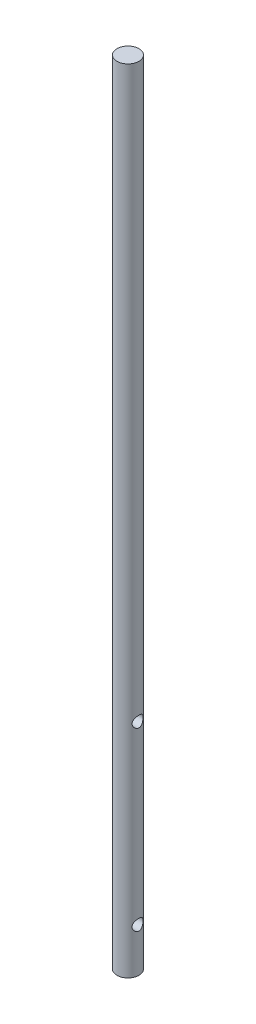
SolidWorks part; units mm, degrees
ref_plane "Front Plane" through (0, 0, 0) normal (0, 0, 1) x (1, 0, 0)
ref_plane "Top Plane" through (0, 0, 0) normal (0, 1, 0) x (1, 0, 0)
ref_plane "Right Plane" through (0, 0, 0) normal (1, 0, 0) x (0, 0, -1)
sketch "Sketch1" plane through (0, 0, 0) normal (0, 1, 0) x (1, 0, 0)
  circle A0 centre (0, 0) radius 6.35
  dimension "D1" = 12.7
extrude "Boss-Extrude1" add sketch "Sketch1" along normal blind 457.2
sketch "Sketch2" plane through (0, 0, 0) normal (1, 0, 0) x (0, 0, -1)
  circle A0 centre (0, 25.4) radius 3.175
  circle A1 centre (0, 127) radius 3.175
  dimension "D1" = 6.35
  dimension "D4" = 6.35
  dimension "D2" = 25.4
  dimension "D3" = 101.6
extrude "Cut-Extrude1" cut sketch "Sketch2" against normal through all both and the other way through all
